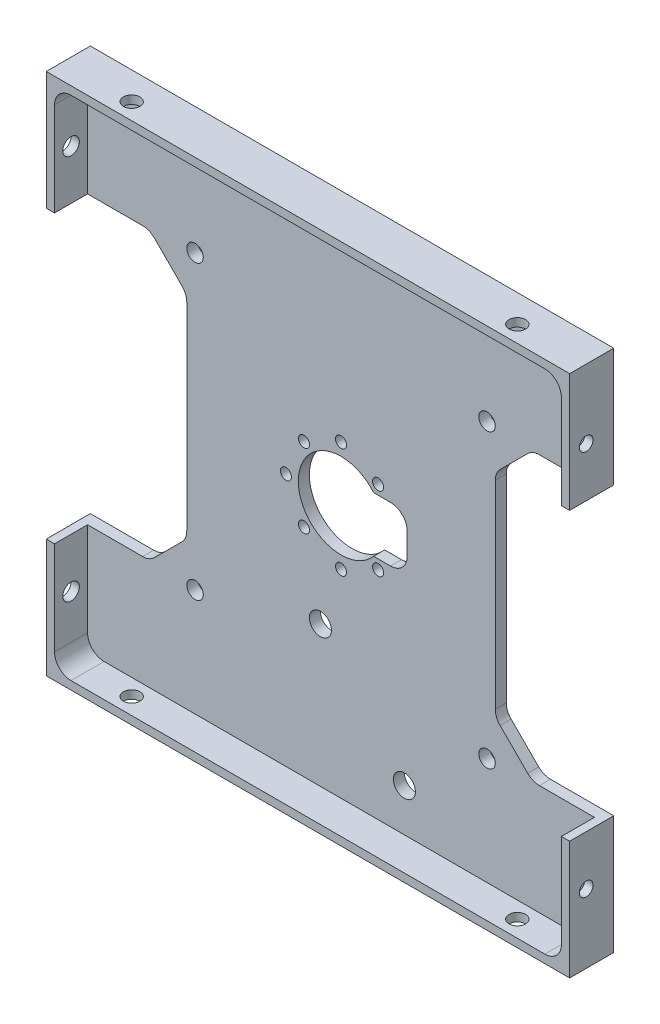
SolidWorks part; units mm, degrees
material "6061-T6 (SS)"
ref_plane "Front" through (0, 0, 0) normal (0, 0, 1) x (1, 0, 0)
ref_plane "Top" through (0, 0, 0) normal (0, 1, 0) x (1, 0, 0)
ref_plane "Right" through (0, 0, 0) normal (1, 0, 0) x (0, 0, -1)
sketch "Sketch1" plane through (0, 0, 0) normal (0, 0, 1) x (1, 0, 0)
  line L1 (-48, -48) -> (48, -48)
  line L2 (-48, -48) -> (-48, 48)
  line L3 (-48, 48) -> (48, 48)
  line L4 (48, -48) -> (48, 48)
  line L5 (-48, -48) -> (48, 48) construction
  line L6 (-48, 48) -> (48, -48) construction
  point P0 (0, 0)
  dimension "D1" = 96
  dimension "D2" = 96
extrude "Boss-Extrude1" add sketch "Sketch1" along normal blind 8
sketch "Sketch2" plane through (0, 0, 8) normal (0, 0, 1) x (1, 0, 0)
  line L1 (46, -46) -> (-46, -46)
  line L2 (46, -46) -> (46, 46)
  line L3 (46, 46) -> (-46, 46)
  line L4 (-46, -46) -> (-46, 46)
  line L5 (46, -46) -> (-46, 46) construction
  line L6 (46, 46) -> (-46, -46) construction
  point P0 (0, 0)
  dimension "D1" = 92
  dimension "D2" = 92
extrude "Component Platform" cut sketch "Sketch2" against normal blind 6
sketch "Sketch3" plane through (0, 0, 2) normal (0, 0, 1) x (1, 0, 0)
  line L1 (-33.8787, -25.1213) -> (-28.8787, -20.1213)
  line L2 (-33.8787, 25.1213) -> (-28.8787, 20.1213)
  line L3 (-28, -18) -> (-28, 18)
  line L4 (-48, -26) -> (-36, -26)
  line L7 (-48, 48) -> (-48, -48) construction
  line L8 (0, -56.7987) -> (0, 73.4321) construction
  line L9 (46, -46) -> (-57.8147, 57.8147) construction
  line L18 (46, 46) -> (-68.5705, -68.5705) construction
  line L23 (-48, 26) -> (-36, 26)
  line L26 (-48, -26) -> (-48, 26)
  line L28 (-48, -48) -> (48, -48) construction
  line L29 (48, -26) -> (48, 26)
  line L30 (48, 26) -> (36, 26)
  line L31 (33.8787, 25.1213) -> (28.8787, 20.1213)
  line L32 (28, -18) -> (28, 18)
  line L33 (33.8787, -25.1213) -> (28.8787, -20.1213)
  line L34 (48, -26) -> (36, -26)
  arc A3 (-28.8787, -20.1213) -> (-28, -18) centre (-31, -18) ccw
  arc A4 (-28.8787, 20.1213) -> (-28, 18) centre (-31, 18) cw
  arc A13 (-33.8787, -25.1213) -> (-36, -26) centre (-36, -23) cw
  arc A15 (-33.8787, 25.1213) -> (-36, 26) centre (-36, 23) ccw
  arc A17 (33.8787, 25.1213) -> (36, 26) centre (36, 23) cw
  arc A18 (28.8787, 20.1213) -> (28, 18) centre (31, 18) ccw
  arc A19 (28.8787, -20.1213) -> (28, -18) centre (31, -18) cw
  arc A20 (33.8787, -25.1213) -> (36, -26) centre (36, -23) ccw
  point P0 (-48, 0)
  point P37 (-48, 0)
  dimension "D2" = 3
  dimension "D3" = 3
  dimension "D4" = 20
  dimension "D6" = 3
  dimension "D7" = 3
  dimension "D8" = 135
  dimension "D5" = 52
  dimension "D9" = 135
  dimension "D10" = 12
  dimension "D11" = 12
  dimension "D12" = 48
extrude "Cable Slots" cut sketch "Sketch3" against normal mid plane 12
sketch "Sketch4" plane through (0, 0, 2) normal (0, 0, 1) x (1, 0, 0)
  circle A0 centre (0, 0) radius 7.75
  dimension "D1" = 15.5
extrude "Center Mass Cut" cut sketch "Sketch4" against normal blind 6
ref_plane "Center Y-Plane" through (0, 0, 0) normal (1, 0, 0) x (0, 0, -1)
ref_plane "Center X-Plane" through (0, 0, 0) normal (0, -1, 0) x (-1, 0, 0)
fillet "Inner Corner Fillets" radius 3 4 edges at (46, -46, 5) (-46, -46, 5) (46, 46, 5) (-46, 46, 5)
sketch "Sketch10" plane through (0, 0, 2) normal (0, 0, 1) x (1, 0, 0)
  line L1 (0, -5) -> (12, -5)
  line L2 (12, -5) -> (12, 5)
  line L3 (12, 5) -> (0, 5)
  line L5 (0, -5) -> (0, 5)
  point P3 (0, 0)
  dimension "D1" = 10
  dimension "D3" = 12
extrude "Motor Cutout" cut sketch "Sketch10" against normal blind 2
fillet "Fillet1" radius 3 2 edges at (12, 5, 1) (12, -5, 1)
sketch "Sketch11" plane through (0, 0, 2) normal (0, 0, 1) x (1, 0, 0)
  line L0 (0, 0) -> (0, 23.9217) construction
  line L1 (0, 0) -> (0, -24.7081) construction
  line L2 (0, 0) -> (-16.3847, 0) construction
  line L3 (0, 0) -> (16.7779, 0) construction
  circle A0 centre (6.72, 6.72) radius 1.05
  circle A1 centre (-6.72, 6.72) radius 1.05
  circle A2 centre (-6.72, -6.72) radius 1.05
  circle A3 centre (6.72, -6.72) radius 1.05
  circle A4 centre (0, 10) radius 1.05
  circle A5 centre (-10, 0) radius 1.05
  circle A6 centre (0, -10) radius 1.05
  dimension "D9" = 2.1
  dimension "D1" = 6.72
  dimension "D2" = 6.72
  dimension "D3" = 6.72
  dimension "D4" = 6.72
  dimension "D5" = 6.72
  dimension "D6" = 6.72
  dimension "D7" = 6.72
  dimension "D8" = 6.72
  dimension "D10" = 10
  dimension "D11" = 10
  dimension "D12" = 10
sketch "Sketch12" plane through (48, 0, 0) normal (1, 0, 0) x (0, 0, -1)
  line L0 (-5, -48) -> (-5, 48) construction
  line L1 (-8, -48) -> (0, -48) construction
  line L2 (-8, 48) -> (0, 48) construction
  line L3 (-8, -48) -> (-8, -26) construction
  dimension "D1" = 3
hole_wizard "M3x0.5 Tapped Hole1" positions "Sketch13" profile "Sketch14" tap size "M3x0.5" standard "ANSI Metric" end condition up to next
sketch "Sketch13" plane through (48, 0, 0) normal (1, 0, 0) x (0, 0, -1)
  line L0 (-5, -48) -> (-5, 48) construction
  point P0 (-5, -35)
  point P4 (-5, 35)
  dimension "D1" = 70
  dimension "D2" = 35
sketch "Sketch14" plane through (48, -35, 5) normal (0, 1, 0) x (0, 0, -1)
  line L0 (0, 0) -> (0, 2)
  line L1 (0, 2) -> (1.25, 2)
  line L2 (1.25, 2) -> (1.25, 0)
  line L5 (1.25, 0) -> (0, 0)
  line L11 (0, -6.35) -> (0, 107.95) construction
  dimension "Thread Major Dia." = 2.5
  dimension "Thru Tap Drill Depth" = 2
sketch "Sketch15" plane through (0, 48, 0) normal (0, 1, 0) x (1, 0, 0)
  line L0 (-48, -5) -> (48, -5) construction
  line L1 (-48, -8) -> (-48, 0) construction
  line L2 (48, -8) -> (48, 0) construction
  line L3 (48, -8) -> (-48, -8) construction
  dimension "D1" = 3
hole_wizard "Ø3.0mm Dowel Hole1" positions "Sketch16" profile "Sketch17" hole size "Ø3.0" standard "ANSI Metric" end condition up to next
sketch "Sketch16" plane through (0, 48, 0) normal (0, 1, 0) x (1, 0, 0)
  line L0 (-48, -5) -> (48, -5) construction
  point P0 (35, -5)
  point P4 (-35, -5)
  dimension "D1" = 70
  dimension "D2" = 35
sketch "Sketch17" plane through (35, 48, 5) normal (1, 0, 0) x (0, 0, 1)
  line L0 (0, 0) -> (0, 2)
  line L1 (0, 2) -> (1.5, 2)
  line L2 (1.5, 2) -> (1.5, 0)
  line L5 (1.5, 0) -> (0, 0)
  line L11 (0, -6.35) -> (0, 107.95) construction
  dimension "Thru Hole Dia." = 3
  dimension "Thru Hole Depth" = 2
mirror "Mirror2" about plane through (0, 0, 0) normal (0, -1, 0) of "Ø3.0mm Dowel Hole1"
sketch "Sketch18" plane through (0, 0, 2) normal (0, 0, 1) x (1, 0, 0)
  line L0 (0, -46) -> (0, 46) construction
  line L1 (-43, -46) -> (43, -46) construction
  line L2 (43, 46) -> (-43, 46) construction
  line L6 (46, -28.5) -> (-46, -28.5) construction
  line L7 (46, -43) -> (46, -26) construction
  line L8 (-46, -26) -> (-46, -43) construction
  line L9 (-28.5, -46) -> (-28.5, 46) construction
  line L10 (-43, -46) -> (43, -46) construction
  dimension "D1" = 17.5
  dimension "D2" = 28.5
hole_wizard "Ø3.0mm Dowel Hole2" positions "Sketch19" profile "Sketch20" hole size "Ø3.0" standard "ANSI Metric" end condition up to next
sketch "Sketch19" plane through (0, 0, 2) normal (0, 0, 1) x (1, 0, 0)
  line L20 (-43, -46) -> (43, -46) construction
  line L21 (-46, -26) -> (-46, -43) construction
  line L26 (43, 46) -> (-43, 46) construction
  line L27 (46, 26) -> (46, 43) construction
  line L28 (46, -43) -> (46, -26) construction
  line L29 (-46, 43) -> (-46, 26) construction
  point P49 (-26.5, -26.5)
  point P56 (-26.5, -26.5)
  point P67 (26.5, -26.5)
  point P70 (26.5, 26.5)
  point P73 (-26.5, 26.5)
  point P83 (26.5, -26.5)
  point P85 (26.5, 26.5)
  point P87 (-26.5, 26.5)
  dimension "D1" = 19.5
  dimension "D2" = 19.5
  dimension "D3" = 19.5
  dimension "D4" = 19.5
  dimension "D5" = 19.5
  dimension "D6" = 19.5
  dimension "D7" = 19.5
  dimension "D8" = 19.5
sketch "Sketch20" plane through (-26.5, -26.5, 2) normal (1, 0, 0) x (0, -1, 0)
  line L0 (0, 0) -> (0, 2)
  line L1 (0, 2) -> (1.5, 2)
  line L2 (1.5, 2) -> (1.5, 0)
  line L5 (1.5, 0) -> (0, 0)
  line L11 (0, -6.35) -> (0, 107.95) construction
  dimension "Thru Hole Dia." = 3
  dimension "Thru Hole Depth" = 2
hole_wizard "Ø2.0mm Dowel Hole1" positions "Sketch23" profile "Sketch24" hole size "Ø2.0" standard "ANSI Metric" end condition up to next
sketch "Sketch23" plane through (0, 0, 2) normal (0, 0, 1) x (1, 0, 0)
  point P0 (6.72, -6.72)
  point P3 (0, -10)
  point P6 (-6.72, -6.72)
  point P9 (-10, 0)
  point P12 (-6.72, 6.72)
  point P15 (0, 10)
  point P18 (6.72, 6.72)
sketch "Sketch24" plane through (6.72, -6.72, 2) normal (1, 0, 0) x (0, -1, 0)
  line L0 (0, 0) -> (0, 2)
  line L1 (0, 2) -> (1, 2)
  line L2 (1, 2) -> (1, 0)
  line L5 (1, 0) -> (0, 0)
  line L11 (0, -6.35) -> (0, 107.95) construction
  dimension "Thru Hole Dia." = 2
  dimension "Thru Hole Depth" = 2
sketch "Sketch25" plane through (0, 0, 2) normal (0, 0, 1) x (1, 0, 0)
  line L0 (0, -46) -> (0, 46) construction
  line L1 (-43, -46) -> (43, -46) construction
  line L2 (43, 46) -> (-43, 46) construction
  line L3 (-46, -38.25) -> (46, -38.25) construction
  line L4 (-46, -26) -> (-46, -43) construction
  line L5 (46, -43) -> (46, -26) construction
  line L6 (-43, -46) -> (43, -46) construction
  point P14 (11.5, -38.25)
  point P15 (-3.74, -20.47)
  dimension "D1" = 7.75
  dimension "D2" = 11.5
  dimension "D3" = 15.24
  dimension "D4" = 17.78
hole_wizard "Ø4.0mm Dowel Hole1" positions "Sketch26" profile "Sketch27" hole size "Ø4.0" standard "ANSI Metric" end condition up to next
sketch "Sketch26" plane through (0, 0, 2) normal (0, 0, 1) x (1, 0, 0)
  point P0 (-3.74, -20.47)
  point P3 (11.5, -38.25)
sketch "Sketch27" plane through (-3.74, -20.47, 2) normal (1, 0, 0) x (0, -1, 0)
  line L0 (0, 0) -> (0, 2)
  line L1 (0, 2) -> (2, 2)
  line L2 (2, 2) -> (2, 0)
  line L5 (2, 0) -> (0, 0)
  line L11 (0, -6.35) -> (0, 107.95) construction
  dimension "Thru Hole Dia." = 4
  dimension "Thru Hole Depth" = 2
sketch "Sketch28" plane through (-48, 0, 0) normal (-1, 0, 0) x (0, 0, 1)
  line L0 (8, 48) -> (8, 26) construction
  line L1 (8, 48) -> (0, 48) construction
  line L2 (5, 48) -> (5, 26) construction
  line L3 (0, 26) -> (8, 26) construction
  point P12 (5, 35)
  dimension "D1" = 13
  dimension "D2" = 3
sketch "Sketch29" plane through (-48, 0, 0) normal (-1, 0, 0) x (0, 0, 1)
  line L0 (8, -26) -> (8, -48) construction
  line L3 (8, -48) -> (0, -48) construction
  line L5 (5, -48) -> (5, -26) construction
  line L6 (0, -26) -> (8, -26) construction
  point P10 (5, -35)
  dimension "D1" = 3
  dimension "D2" = 13
hole_wizard "Ø3.0mm Dowel Hole3" positions "3DSketch1" profile "Sketch30" hole size "Ø3.0" standard "ANSI Metric" end condition up to next
sketch3d "3DSketch1"
  point P0 (-48, 35, 5)
  point P3 (-48, -35, 5)
sketch "Sketch30" plane through (-48, 35, 5) normal (0, 1, 0) x (0, 0, 1)
  line L0 (0, 0) -> (0, 2)
  line L1 (0, 2) -> (1.5, 2)
  line L2 (1.5, 2) -> (1.5, 0)
  line L5 (1.5, 0) -> (0, 0)
  line L11 (0, -6.35) -> (0, 107.95) construction
  dimension "Thru Hole Dia." = 3
  dimension "Thru Hole Depth" = 2
sketch "Sketch34" plane through (0, 0, 0) normal (0, 0, -1) x (-1, 0, 0)
  line L1 (-47.5, -47.5) -> (47.5, -47.5)
  line L2 (-47.5, -47.5) -> (-47.5, 47.5)
  line L3 (-47.5, 47.5) -> (47.5, 47.5)
  line L4 (47.5, -47.5) -> (47.5, 47.5)
  line L5 (-47.5, -47.5) -> (47.5, 47.5) construction
  line L6 (-47.5, 47.5) -> (47.5, -47.5) construction
  point P0 (0, 0)
  dimension "D1" = 95
  dimension "D2" = 95
extrude "Cut-Extrude1" cut sketch "Sketch34" against normal blind 10 flip side to cut
